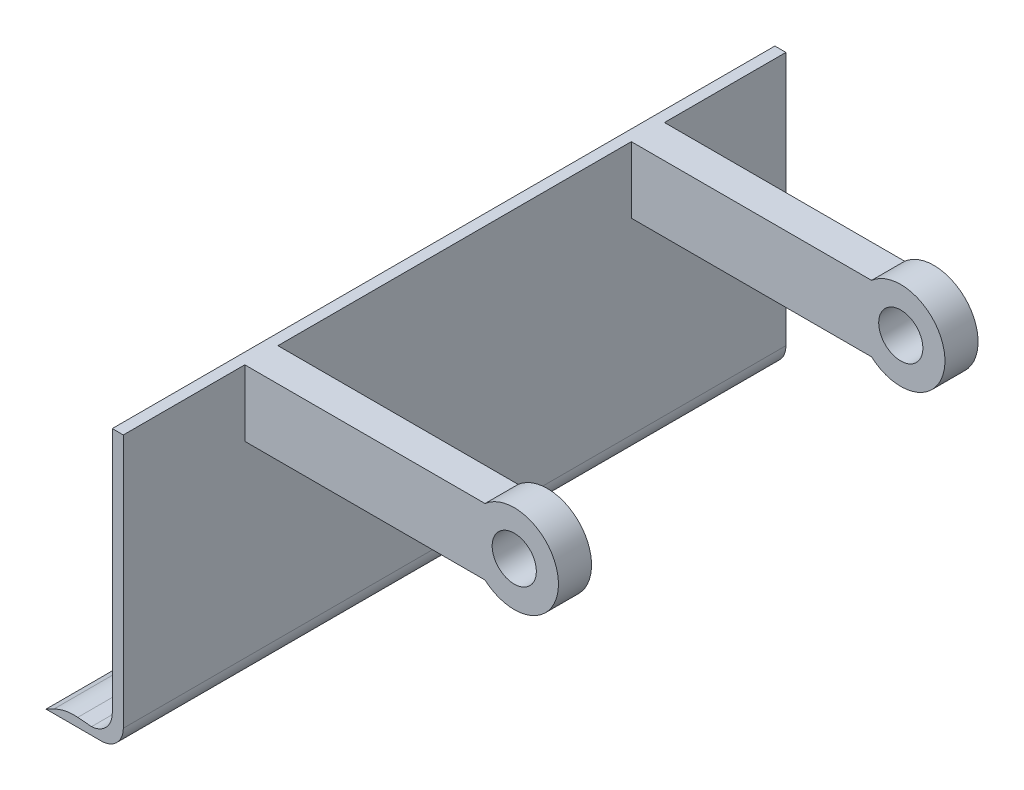
SolidWorks part; units mm, degrees
ref_plane "Plan de face" through (0, 0, 0) normal (0, 0, 1) x (1, 0, 0)
ref_plane "Plan de dessus" through (0, 0, 0) normal (0, 1, 0) x (1, 0, 0)
ref_plane "Plan de droite" through (0, 0, 0) normal (1, 0, 0) x (0, 0, -1)
sketch "Esquisse1" plane through (0, 0, 0) normal (0, 0, 1) x (1, 0, 0)
  line L0 (-5, 35) -> (-5, 13.418)
  line L1 (-14.387, 3.4368) -> (-20.6199, 3.9625)
  line L2 (0, 30) -> (0, 125)
  line L3 (0, 125) -> (-5, 125)
  line L4 (-5, 35) -> (-5, 125)
  line L5 (-31.4173, 1.8348) -> (-35, 0)
  line L6 (-35, 0) -> (-10, 0)
  line L7 (0, 10) -> (0, 30)
  arc A0 (-31.4173, 1.8348) -> (-20.6199, 3.9625) centre (-22.3009, -15.9667) cw
  arc A1 (-10, 0) -> (0, 10) centre (-10, 10) ccw
  arc A2 (-5, 13.418) -> (-14.387, 3.4368) centre (-15, 13.418) cw
  point P13 (0, 0)
  dimension "D2" = 5
  dimension "D1" = 10
  dimension "D3" = 20
  dimension "D4" = 10
  dimension "D5" = 125
  dimension "D6" = 35
extrude "Boss.-Extru.1" add sketch "Esquisse1" along normal blind 300
sketch "Esquisse3" plane through (0, 0, 0) normal (1, 0, 0) x (0, 0, -1)
  line L1 (-300, 125) -> (0, 125) construction
  line L3 (-230, 125) -> (-245, 125)
  line L4 (-230, 125) -> (-230, 95)
  line L5 (-230, 95) -> (-245, 95)
  line L6 (-245, 125) -> (-245, 95)
  line L7 (-70, 125) -> (-55, 125)
  line L8 (-70, 125) -> (-70, 95)
  line L12 (-70, 95) -> (-55, 95)
  line L13 (-55, 125) -> (-55, 95)
  line L15 (0, 10) -> (0, 125) construction
  dimension "D1" = 160
  dimension "D2" = 15
  dimension "D3" = 30
  dimension "D4" = 30
  dimension "D5" = 15
  dimension "D6" = 55
extrude "Boss.-Extru.2" add sketch "Esquisse3" along normal blind 115
sketch "Esquisse4" plane through (0, 0, 245) normal (0, 0, 1) x (1, 0, 0)
  line L0 (115, 125) -> (115, 95) construction
  line L1 (115, 110) -> (160.4893, 110) construction
  circle A0 centre (122, 110) radius 20
  dimension "D1" = 7
  dimension "D2" = 40
extrude "Boss.-Extru.3" add sketch "Esquisse4" against normal up to surface (15 mm away) up to face at (57.5, 110, 230)
sketch "Esquisse5" plane through (0, 0, 245) normal (0, 0, 1) x (1, 0, 0)
  circle A0 centre (122, 110) radius 10
  dimension "D1" = 20
sketch "Esquisse6" plane through (0, 0, 70) normal (0, 0, 1) x (1, 0, 0)
  circle A0 centre (122, 110) radius 20
extrude "Boss.-Extru.4" add sketch "Esquisse6" against normal up to surface (15 mm away) up to face at (57.5, 110, 55)
extrude "Enlèv. mat.-Extru.1" cut sketch "Esquisse5" against normal through all contours A0
